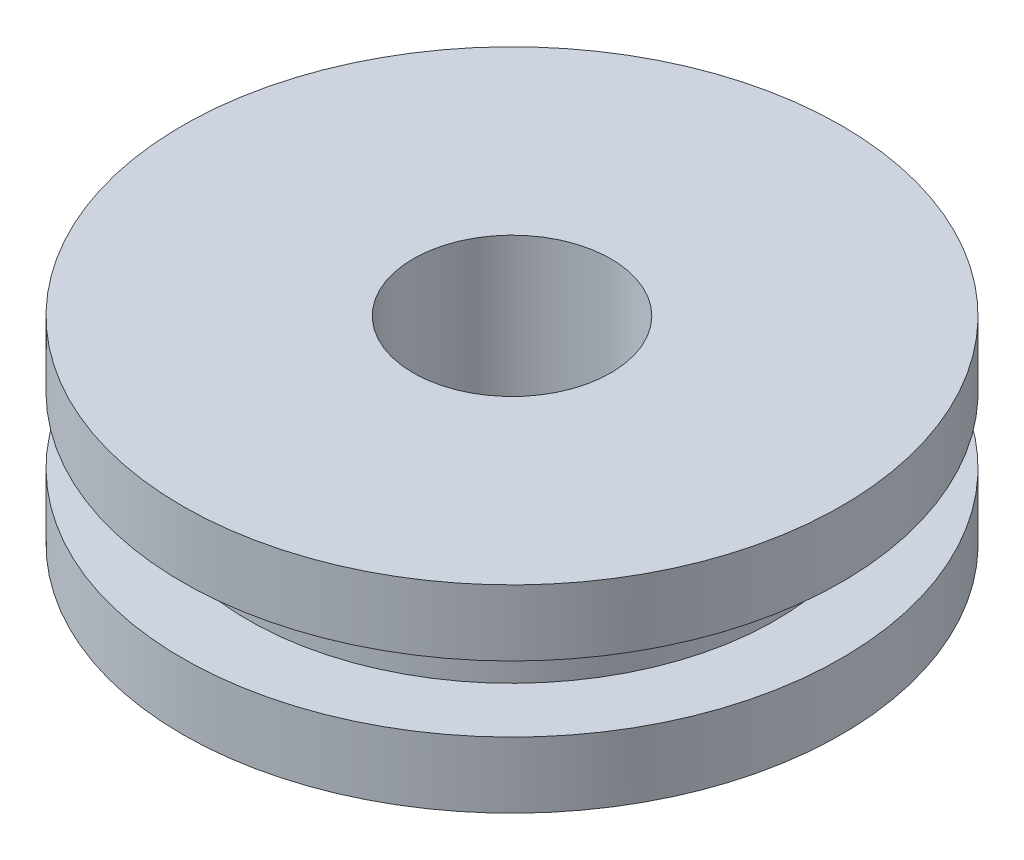
SolidWorks part; units mm, degrees
ref_plane "前视基准面" through (0, 0, 0) normal (0, 0, 1) x (1, 0, 0)
ref_plane "上视基准面" through (0, 0, 0) normal (0, 1, 0) x (1, 0, 0)
ref_plane "右视基准面" through (0, 0, 0) normal (1, 0, 0) x (0, 0, -1)
sketch "草图1" plane through (0, 0, 0) normal (0, 1, 0) x (1, 0, 0)
  circle A0 centre (0, 0) radius 5
  dimension "D1" = 10
extrude "凸台-拉伸1" add sketch "草图1" along normal blind 3
sketch "草图2" plane through (0, 3, 0) normal (0, 1, 0) x (1, 0, 0)
  circle A0 centre (0, 0) radius 1.5
  dimension "D1" = 3
extrude "切除-拉伸1" cut sketch "草图2" against normal blind 11
ref_plane "基准面1" through (0, 1.5, 0) normal (0, -1, 0) x (-1, 0, 0)
sketch "草图3" plane through (0, 1.5, 0) normal (0, -1, 0) x (-1, 0, 0)
  circle A0 centre (0, 0) radius 5
  circle A1 centre (0, 0) radius 4
  dimension "D1" = 8
extrude "切除-拉伸3" cut sketch "草图3" against normal mid plane 1 contours A0 | A1
